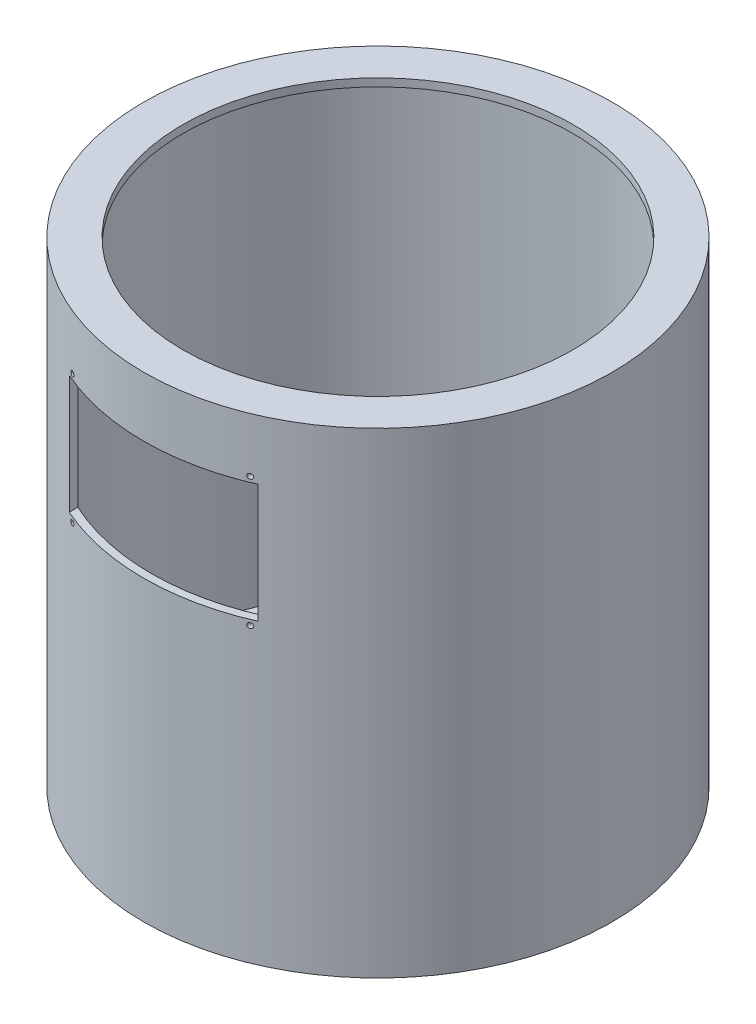
SolidWorks part; units mm, degrees
ref_plane "Front Plane" through (0, 0, 0) normal (0, 0, 1) x (1, 0, 0)
ref_plane "Top Plane" through (0, 0, 0) normal (0, 1, 0) x (1, 0, 0)
ref_plane "Right Plane" through (0, 0, 0) normal (1, 0, 0) x (0, 0, -1)
sketch "Sketch1" plane through (0, 0, 0) normal (0, 1, 0) x (1, 0, 0)
  circle A0 centre (0, 0) radius 150
  circle A1 centre (0, 0) radius 125
  dimension "D1" = 300
  dimension "D2" = 250
extrude "Boss-Extrude1" add sketch "Sketch1" along normal blind 5
sketch "Sketch2" plane through (0, 5, 0) normal (0, 1, 0) x (1, 0, 0)
  circle A0 centre (0, 0) radius 150 construction
  circle A1 centre (0, 0) radius 150
  circle A2 centre (0, 0) radius 145
  dimension "D1" = 5
extrude "Boss-Extrude2" add sketch "Sketch2" along normal blind 300
sketch "Sketch3" plane through (0, 305, 0) normal (0, 1, 0) x (1, 0, 0)
  circle A0 centre (0, 0) radius 150 construction
  circle A1 centre (0, 0) radius 150
  circle A2 centre (0, 0) radius 125
  dimension "D1" = 25
extrude "Boss-Extrude3" add sketch "Sketch3" against normal blind 5
sketch "Sketch5" plane through (0, 0, 0) normal (0, 0, 1) x (1, 0, 0)
  line L0 (-150, 152.5) -> (150, 152.5) construction
  line L1 (-150, 305) -> (-150, 0) construction
  line L2 (150, 0) -> (150, 305) construction
  line L3 (0, 305) -> (0, 152.5) construction
  line L4 (150, 305) -> (-150, 305) construction
  line L6 (-60.5, 266.75) -> (60.5, 266.75)
  line L7 (-60.5, 266.75) -> (-60.5, 190.75)
  line L8 (-60.5, 190.75) -> (60.5, 190.75)
  line L9 (60.5, 266.75) -> (60.5, 190.75)
  line L10 (-60.5, 266.75) -> (60.5, 190.75) construction
  line L11 (-60.5, 190.75) -> (60.5, 266.75) construction
  point P10 (0, 228.75)
  dimension "D1" = 76
  dimension "D2" = 121
extrude "Cut-Extrude1" cut sketch "Sketch5" along normal up to next
sketch "Sketch7" plane through (0, 0, 0) normal (0, 0, 1) x (1, 0, 0)
  line L0 (60.5, 228.75) -> (-60.5, 228.75) construction
  line L1 (60.5, 266.75) -> (60.5, 190.75) construction
  line L2 (-60.5, 190.75) -> (-60.5, 266.75) construction
  line L4 (-56.95, 270.15) -> (56.95, 270.15) construction
  line L5 (-56.95, 270.15) -> (-56.95, 187.35) construction
  line L6 (-56.95, 187.35) -> (56.95, 187.35) construction
  line L7 (56.95, 270.15) -> (56.95, 187.35) construction
  line L8 (-56.95, 270.15) -> (56.95, 187.35) construction
  line L9 (-56.95, 187.35) -> (56.95, 270.15) construction
  circle A0 centre (56.95, 270.15) radius 1.6
  circle A1 centre (56.95, 187.35) radius 1.6
  circle A2 centre (-56.95, 270.15) radius 1.6
  circle A3 centre (-56.95, 187.35) radius 1.6
  point P6 (0, 228.75)
  dimension "D3" = 3.2
  dimension "D1" = 82.8
  dimension "D2" = 113.9
extrude "Cut-Extrude2" cut sketch "Sketch7" along normal up to next
